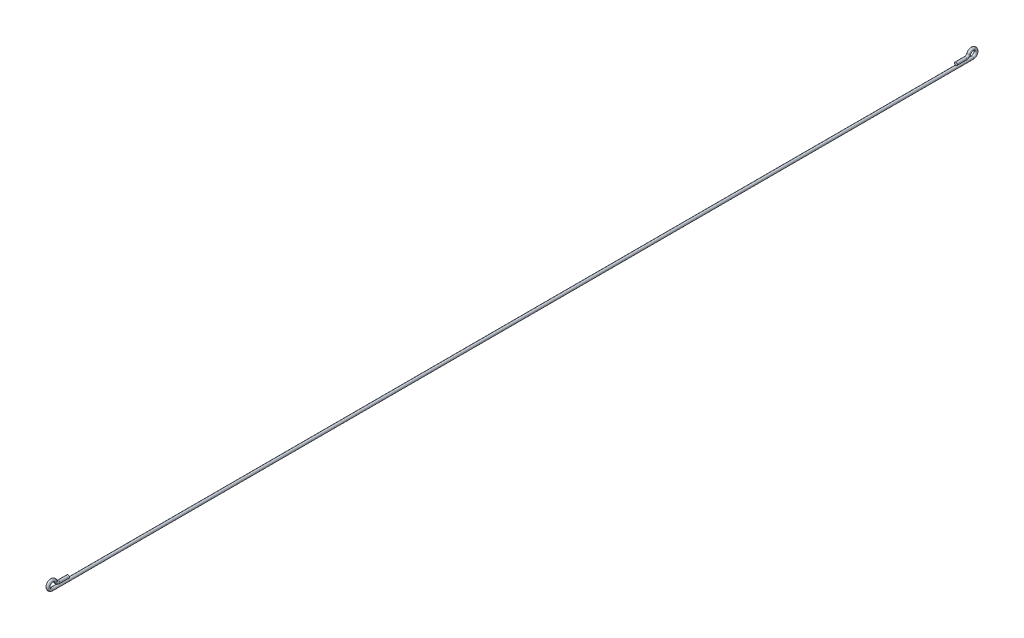
SolidWorks part; units mm, degrees
ref_plane "Front Plane" through (0, 0, 0) normal (0, 0, 1) x (1, 0, 0)
ref_plane "Top Plane" through (0, 0, 0) normal (0, 1, 0) x (1, 0, 0)
ref_plane "Right Plane" through (0, 0, 0) normal (1, 0, 0) x (0, 0, -1)
sketch "Sketch1" plane through (0, 0, 0) normal (0, 0, 1) x (1, 0, 0)
  circle A0 centre (0, 0) radius 1.5
  dimension "D1" = 3
sketch "Sketch2" plane through (0, 0, 0) normal (1, 0, 0) x (0, 0, -1)
  line L0 (-17.4162, -3) -> (472.5838, -3)
  line L1 (-10, 0) -> (0, 0)
  arc A0 (-17.4162, -3) -> (-13.7081, 2.5) centre (-17.4162, 1) cw
  arc A1 (-13.7081, 2.5) -> (-10, 0) centre (-10, 4) ccw
  dimension "D3" = 4
  dimension "D4" = 4
  dimension "D1" = 490
  dimension "D2" = 10
  dimension "D5" = 3
sweep "Sweep1" add profiles "Sketch1" path "Sketch2"
mirror "Mirror1" about plane through (0, -3, -472.5838) normal (0, 0, -1) of "Sweep1"
